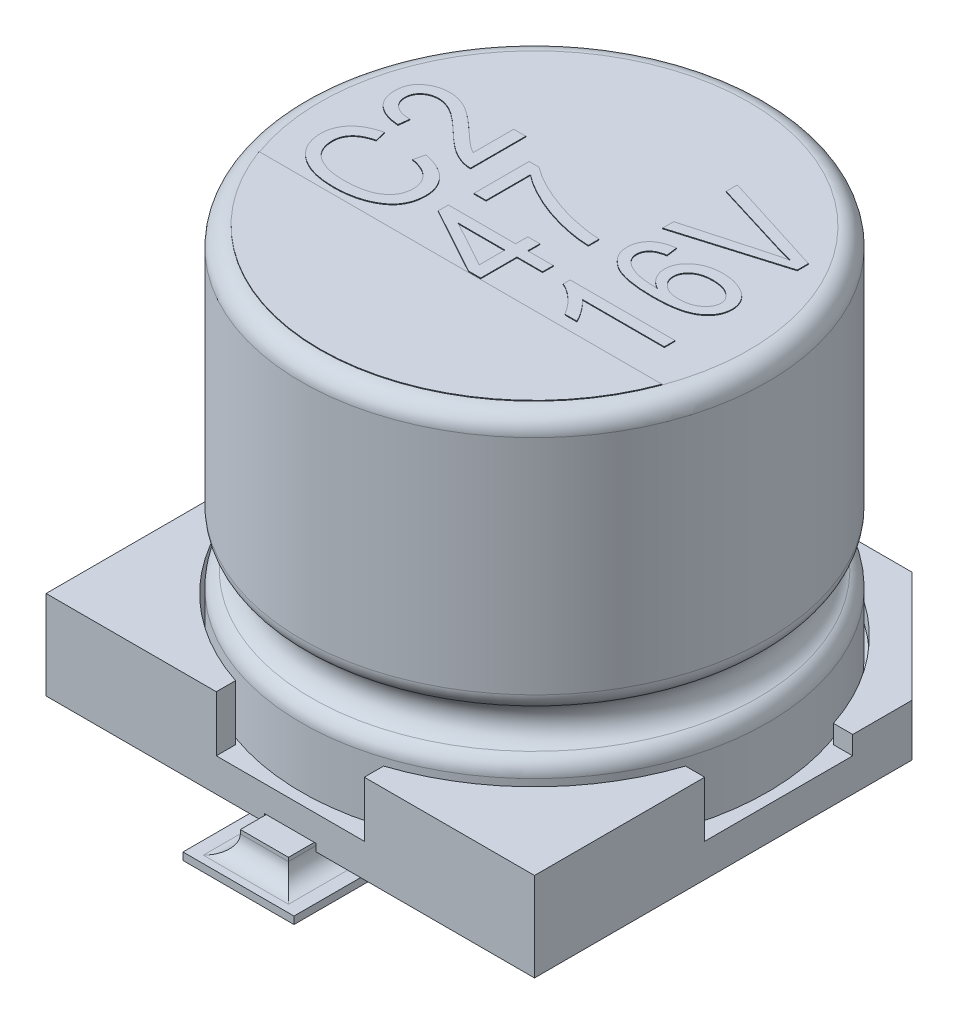
SolidWorks part; units mm, degrees
material "PA Type 6"
ref_plane "Front Plane" through (0, 0, 0) normal (0, 0, 1) x (1, 0, 0)
ref_plane "Top Plane" through (0, 0, 0) normal (0, 1, 0) x (1, 0, 0)
ref_plane "Right Plane" through (0, 0, 0) normal (1, 0, 0) x (0, 0, -1)
ref_plane "Plane1" through (0, 0.3, 0) normal (0, 1, 0) x (1, 0, 0)
sketch "Sketch1" plane through (0, 0.3, 0) normal (0, 1, 0) x (1, 0, 0)
  line L0 (-55, 0) -> (55, 0) construction
  line L1 (-3.3, -3.3) -> (3.3, -3.3)
  line L2 (-3.3, -3.3) -> (-3.3, 3.3)
  line L3 (-3.3, 3.3) -> (3.3, 3.3)
  line L4 (3.3, -3.3) -> (3.3, 3.3)
  line L5 (0, -55) -> (0, 55) construction
  dimension "D1" = 6.6
  dimension "D2" = 6.6
  dimension "D3" = 3.3
  dimension "D4" = 3.3
extrude "Boss-Extrude1" add sketch "Sketch1" along normal blind 1.2
sketch "Sketch2" plane through (0, 1.5, 0) normal (0, 1, 0) x (1, 0, 0)
  line L0 (-3.3, 1) -> (-3.0397, 1)
  line L1 (-3.3, 3.3) -> (-3.3, -3.3) construction
  line L2 (3.3, -3.3) -> (3.3, 3.3) construction
  line L3 (3.3, 1) -> (3.3, -1)
  line L4 (3.3, -1) -> (3.0397, -1)
  line L5 (-3.3, -1) -> (-3.3, 1)
  line L6 (3.3, 3.3) -> (-3.3, 3.3) construction
  line L7 (-1, 3.3) -> (1, 3.3)
  line L8 (-1, 3.3) -> (-1, 3.0397)
  line L9 (-1, -3.3) -> (1, -3.3)
  line L10 (1, 3.3) -> (1, 3.0397)
  line L11 (-3.3, -3.3) -> (3.3, -3.3) construction
  line L15 (-3.0397, -1) -> (-3.3, -1)
  line L16 (-1, -3.0397) -> (-1, -3.3)
  line L17 (1, -3.0397) -> (1, -3.3)
  line L19 (3.0397, 1) -> (3.3, 1)
  line L20 (-55, 0) -> (55, 0) construction
  line L22 (0, -55) -> (0, 55) construction
  arc A0 (3.0397, 1) -> (1, 3.0397) centre (0, 0) ccw
  arc A1 (-1, 3.0397) -> (-3.0397, 1) centre (0, 0) ccw
  arc A2 (-3.0397, -1) -> (-1, -3.0397) centre (0, 0) ccw
  arc A3 (1, -3.0397) -> (3.0397, -1) centre (0, 0) ccw
  dimension "D1" = 6.4
  dimension "D2" = 1
  dimension "D3" = 1
  dimension "D4" = 1
extrude "Cut-Extrude1" cut sketch "Sketch2" against normal blind 0.75
sketch "Sketch3" plane through (0, 0, 0) normal (1, 0, 0) x (0, 0, -1)
  line L0 (0, 55) -> (0, -55) construction
  line L1 (3.3, 1.5) -> (0, 1.5)
  line L2 (3.3, 1.5) -> (3.3, 1)
  line L3 (3.3, 1) -> (0, 1)
  line L4 (0, 1.5) -> (0, 1)
  dimension "D1" = 0.5
extrude "Cut-Extrude2" cut sketch "Sketch3" against normal through all and the other way through all
chamfer "Chamfer1" distance 1.5 angle 45 2 edges at (-3.3, 0.65, -3.3) (3.3, 0.65, -3.3)
sketch "Sketch4" plane through (0, 0, 0) normal (1, 0, 0) x (0, 0, -1)
  line L0 (0, 0) -> (0, 7.4696) construction
  line L1 (0, 55) -> (0, -55) construction
  line L2 (0, 0.75) -> (0, 5.8)
  line L3 (-1, 0.75) -> (1, 0.75) construction
  line L4 (0, 5.8) -> (-2.9, 5.8)
  line L5 (-3.15, 5.55) -> (-3.15, 2.5399)
  line L6 (-3.15, 1.5601) -> (-3.15, 0.75)
  line L7 (-3.15, 0.75) -> (0, 0.75)
  line L9 (55, 0) -> (-55, 0) construction
  arc A0 (-2.9, 5.8) -> (-3.15, 5.55) centre (-2.9, 5.55) ccw
  arc A1 (-3.0136, 2.3172) -> (-3.0136, 1.7828) centre (-3.15, 2.05) cw
  arc A2 (-3.0136, 1.7828) -> (-3.15, 1.5601) centre (-2.9, 1.5601) ccw
  arc A3 (-3.15, 2.5399) -> (-3.0136, 2.3172) centre (-2.9, 2.5399) ccw
  point P20 (-3.15, 1.75)
  dimension "D2" = 0.3
  dimension "D5" = 0.25
  dimension "D6" = 0.25
  dimension "D1" = 6.3
  dimension "D3" = 1
  dimension "D4" = 5.8
revolve "Revolve1" add sketch "Sketch4" angle 360 about L0
sketch "Sketch6" plane through (0, 0.3, 0) normal (0, -1, 0) x (1, 0, 0)
  line L0 (0, -55) -> (0, 55) construction
  line L1 (-0.325, -1.225) -> (-0.325, -3.65)
  line L2 (-0.325, -3.65) -> (0.325, -3.65)
  line L3 (0.325, -3.65) -> (0.325, -1.225)
  line L4 (-0.325, 1.225) -> (-0.325, 3.65)
  line L5 (-0.325, 3.65) -> (0.325, 3.65)
  line L6 (0.325, 3.65) -> (0.325, 1.225)
  line L7 (55, 0) -> (-55, 0) construction
  line L8 (-3.3, 3.3) -> (3.3, 3.3) construction
  line L9 (1.8, -3.3) -> (-1.8, -3.3) construction
  arc A0 (-0.325, 1.225) -> (0.325, 1.225) centre (0, 1.225) ccw
  arc A1 (0.325, -1.225) -> (-0.325, -1.225) centre (0, -1.225) ccw
  dimension "D1" = 0.65
  dimension "D2" = 2.45
  dimension "D3" = 1.225
  dimension "D4" = 0.35
  dimension "D5" = 0.35
sketch "Sketch7" plane through (0, 0.3, 0) normal (0, -1, 0) x (1, 0, 0)
  line L0 (-0.35, 3.3) -> (0.35, 3.3)
  line L1 (-3.3, 3.3) -> (3.3, 3.3) construction
  line L2 (0.35, 3.3) -> (0.4987, 1.2614)
  line L3 (-0.4987, 1.2614) -> (-0.35, 3.3)
  line L4 (-0.35, -3.3) -> (0.35, -3.3)
  line L5 (1.8, -3.3) -> (-1.8, -3.3) construction
  line L6 (-0.4987, -1.2614) -> (-0.35, -3.3)
  line L7 (0.4987, -1.2614) -> (0.35, -3.3)
  line L8 (0, -55) -> (0, 55) construction
  arc A0 (-0.4987, 1.2614) -> (0.4987, 1.2614) centre (0, 1.225) ccw
  arc A1 (0.4987, -1.2614) -> (-0.4987, -1.2614) centre (0, -1.225) ccw
  dimension "D3" = 1
  dimension "D1" = 0.7
  dimension "D2" = 0.35
extrude "Cut-Extrude3" cut sketch "Sketch7" against normal blind 0.1
extrude "Boss-Extrude4" add sketch "Sketch6" against normal blind 0.1 and the other way blind 0.3
sketch "Sketch8" plane through (0, 0.3, 0) normal (0, -1, 0) x (1, 0, 0)
  line L0 (0, -55) -> (0, 55) construction
  line L1 (-2, 2) -> (2, 2) construction
  line L2 (-2, 2) -> (-2, -2) construction
  line L3 (-2, -2) -> (2, -2) construction
  line L4 (2, 2) -> (2, -2) construction
  line L5 (55, 0) -> (-55, 0) construction
  circle A0 centre (-2, 2) radius 0.5
  circle A1 centre (2, 2) radius 0.5
  circle A2 centre (2, -2) radius 0.5
  circle A3 centre (-2, -2) radius 0.5
  dimension "D1" = 1
  dimension "D2" = 2
  dimension "D3" = 2
  dimension "D4" = 2
  dimension "D5" = 2
extrude "Boss-Extrude5" add sketch "Sketch8" along normal blind 0.3
sketch "Sketch9" plane through (0, 0, 0) normal (0, 1, 0) x (1, 0, 0)
  line L0 (-3.19, 0) -> (3.19, 0) construction
  line L1 (-0.75, 4) -> (0.75, 4)
  line L2 (-0.75, 4) -> (-0.75, 2)
  line L3 (-0.75, 2) -> (0.75, 2)
  line L4 (0.75, 4) -> (0.75, 2)
  line L5 (-0.75, -2) -> (0.75, -2)
  line L6 (-0.75, -2) -> (-0.75, -4)
  line L7 (-0.75, -4) -> (0.75, -4)
  line L8 (0.75, -2) -> (0.75, -4)
  line L9 (0, -3.19) -> (0, 3.19) construction
  dimension "D1" = 2
  dimension "D2" = 4
  dimension "D3" = 1.5
  dimension "D4" = 0.75
  dimension "D5" = 4
extrude "Boss-Extrude6" add sketch "Sketch9" along normal blind 0.1
fillet "Fillet1" radius 0.25 6 edges at (-0.325, 0.1, -2.825) (0, 0.1, -3.65) (0.325, 0.1, -2.825) (-0.325, 0.1, 2.825) (0.325, 0.1, 2.825) (0, 0.1, 3.65)
sketch "Sketch10" plane through (0, 5.8, 0) normal (0, 1, 0) x (1, 0, 0)
  line L0 (-2.7221, -1) -> (2.7221, -1)
  line L1 (-3.19, 0) -> (3.19, 0) construction
  line L2 (-1.1, -1) -> (-1.1, 2) construction
  line L3 (0, -3.19) -> (0, 3.19) construction
  line L4 (0.6, -1) -> (0.6, 2) construction
  line L6 (2.3, -1) -> (2.3, 2) construction
  circle A0 centre (0, 0) radius 2.9 construction
  arc A1 (-2.7221, -1) -> (2.7221, -1) centre (0, 0) ccw
  text T0 "C2" font "Arial Narrow" height 1.4
  text T1 "47" font "Arial Narrow" height 1.4
  text T2 "16V" font "Arial Narrow" height 1.4
  dimension "D1" = 1
  dimension "D2" = 1.1
  dimension "D3" = 1.7
  dimension "D4" = 1.7
  dimension "D5" = 3
extrude "Boss-Extrude7" add sketch "Sketch10" along normal blind 0.01
